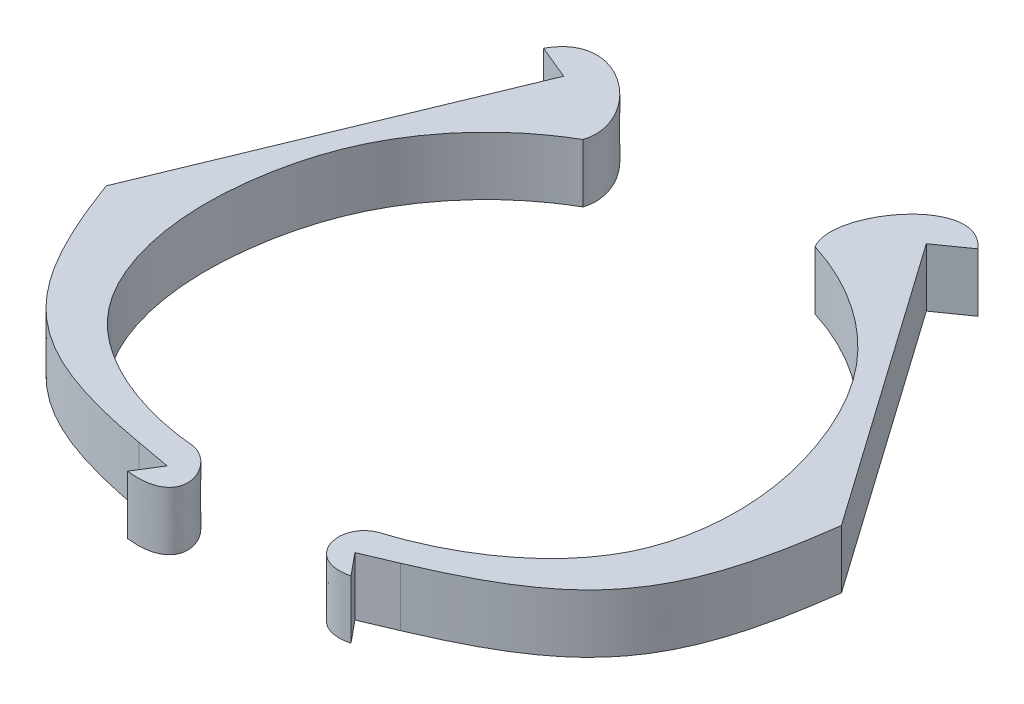
SolidWorks part; units mm, degrees
ref_plane "Front Plane" through (0, 0, 0) normal (0, 0, 1) x (1, 0, 0)
ref_plane "Top Plane" through (0, 0, 0) normal (0, 1, 0) x (1, 0, 0)
ref_plane "Right Plane" through (0, 0, 0) normal (1, 0, 0) x (0, 0, -1)
sketch "Sketch1" plane through (0, 0, 0) normal (0, 1, 0) x (1, 0, 0)
  line L0 (-28.4912, -34.8317) -> (27.7272, -35.443) construction
  line L1 (-33.4866, 46.7493) -> (-56.4037, -8.7017)
  line L2 (-39.3455, 49.1707) -> (-33.4866, 46.7493)
  line L3 (-12.2615, -49.1812) -> (-9.6471, -45)
  line L4 (-9.6471, -45) -> (-15.5351, -43.9324)
  line L5 (4.971, -44.7246) -> (0, 0) construction
  line L6 (19.2928, -41.7834) -> (24.8027, -39.449)
  line L7 (22.4041, -45.5654) -> (19.2928, -41.7834)
  line L8 (27.5883, 56.6101) -> (22.4041, 52.9614)
  line L9 (22.4041, 52.9614) -> (56.9378, 3.8959)
  circle A0 centre (0, 0) radius 45 construction
  spline S0 degree 3 poles (-22.4515, 38.9991) (-26.862, 36.4694) (-33.6272, 30.8347) (-41.5824, 19.0431) (-45.5815, 4.4703) (-45.4301, -12.1667) (-36.9497, -32.8461) (-20.1316, -39.0042) (-10.2545, -39.8366) knots 0 0 0 0 0.143153 0.245275 0.396894 0.561689 0.708961 1 1 1 1
  spline S1 degree 3 poles (-22.4515, 38.9991) (-19.909, 46.6655) (-34.1305, 58.8215) (-39.3455, 49.1707) knots 0 0 0 0 1 1 1 1
  spline S2 degree 3 poles (-56.4037, -8.7017) (-47.6194, -32.5172) (-39.472, -39.5921) (-15.5351, -43.9324) knots 0 0 0 0 1 1 1 1
  spline S3 degree 3 poles (-10.2545, -39.8366) (-5.1995, -41.0135) (-1.6943, -50.4188) (-12.2615, -49.1812) knots 0 0 0 0 1 1 1 1
  spline S4 degree 3 poles (18.7516, -36.6127) (13.1133, -38.3025) (15.3452, -47.3805) (22.4041, -45.5654) knots 0 0 0 0 1 1 1 1
  spline S5 degree 3 poles (56.9378, 3.8959) (53.5973, -21.2672) (47.2023, -29.9585) (24.8027, -39.449) knots 0 0 0 0 1 1 1 1
  spline S6 degree 3 poles (13.3401, 42.9772) (9.1762, 49.8982) (20.3815, 64.8803) (27.5883, 56.6101) knots 0 0 0 0 1 1 1 1
  spline S7 degree 3 poles (13.3401, 42.9772) (18.1984, 41.4778) (26.0358, 37.4661) (36.386, 27.709) (43.4874, 14.3701) (46.9929, -1.8942) (43.2603, -23.931) (28.2049, -33.6317) (18.7516, -36.6127) knots 0 0 0 0 0.143153 0.245275 0.396894 0.561689 0.708961 1 1 1 1
  point P22 (10.7647, -43.6935)
  point P23 (7.2973, -45)
  point P46 (0, 0)
  point P47 (0, 0)
  point P48 (-14.2528, -50.0721)
  point P49 (24.4208, -45.6178)
  point P50 (23.1631, -46.4038)
  point P51 (-12.2615, -49.1812)
  point P52 (22.4041, -45.5654)
  dimension "D1" = 90
  dimension "D2" = 60
extrude "Boss-Extrude1" add sketch "Sketch1" along normal blind 10
